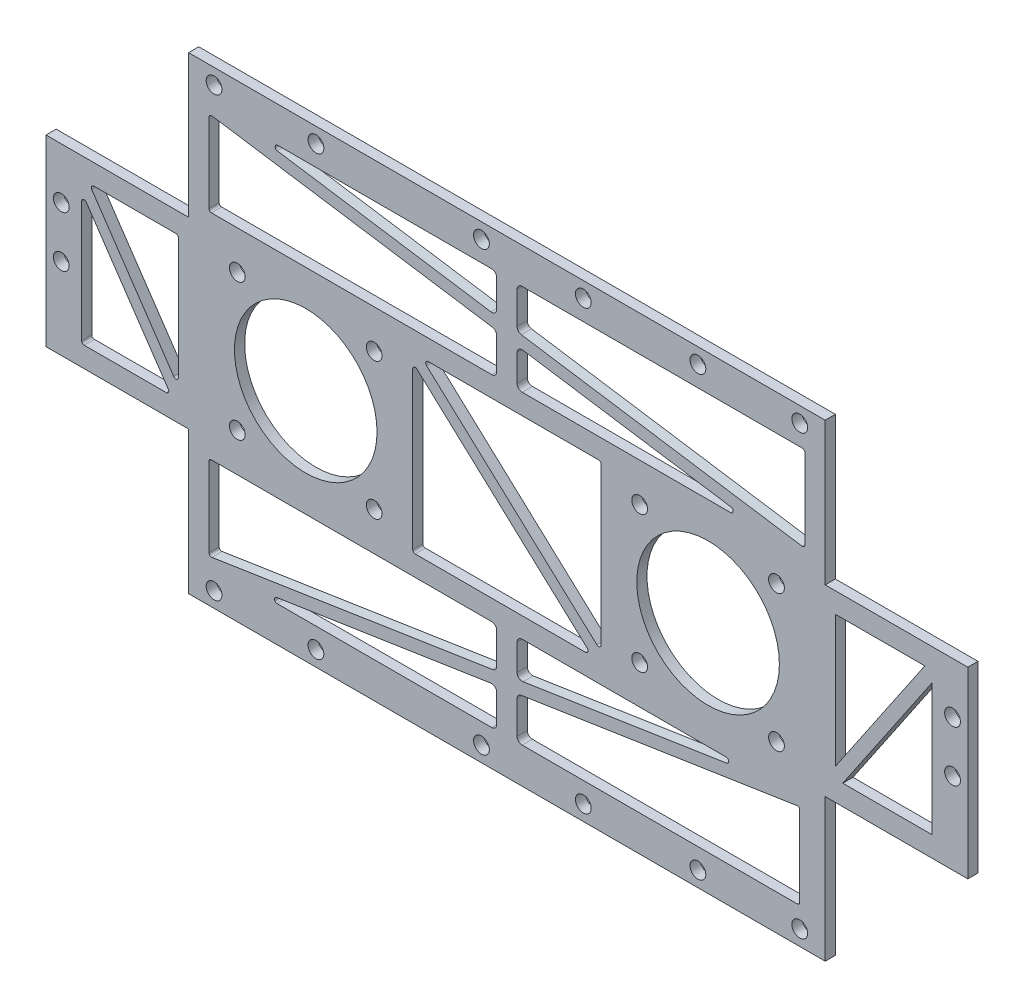
SolidWorks part; units mm, degrees
material "Thornel Mat VMA"
ref_plane "前视基准面" through (0, 0, 0) normal (0, 0, 1) x (1, 0, 0)
ref_plane "上视基准面" through (0, 0, 0) normal (0, 1, 0) x (1, 0, 0)
ref_plane "右视基准面" through (0, 0, 0) normal (1, 0, 0) x (0, 0, -1)
sketch "草图1" plane through (0, 0, 0) normal (0, 0, 1) x (1, 0, 0)
  line L0 (-39.5, 0) -> (39.5, 0) construction
  line L7 (-62.5, -32.4324) -> (70.1149, 36.3839) construction
  line L8 (-92.5, -48) -> (-80.6781, -41.8654) construction
  line L9 (-39.5, 0) -> (-52.935, -13.435) construction
  line L10 (-39.5, 0) -> (-39.5, -19) construction
  line L11 (-52.935, 13.435) -> (-26.065, -13.435) construction
  line L12 (-39.5, 0) -> (-26.065, 13.435) construction
  line L13 (26.065, 13.435) -> (39.5, 0) construction
  line L14 (39.5, 0) -> (52.935, -13.435) construction
  line L15 (39.5, 0) -> (39.5, -24.0416) construction
  line L16 (26.065, -13.435) -> (39.5, 0) construction
  line L17 (39.5, 0) -> (52.935, 13.435) construction
  line L18 (39.5, 0) -> (63.5416, 0) construction
  line L19 (-90.5, 18) -> (-90.5, -18)
  line L20 (-62.5, -46) -> (62.5, -46)
  line L21 (90.5, 18) -> (90.5, -18)
  line L22 (-62.5, 46) -> (62.5, 46)
  line L23 (62.5, -46) -> (62.5, 46) construction
  line L24 (-62.5, -46) -> (-62.5, 46) construction
  line L25 (0, 48) -> (0, -63.7675) construction
  line L26 (-81.1063, 14) -> (-65, 14)
  line L27 (-20, -40) -> (20, -40) construction
  line L28 (-20, -40) -> (-20, -46) construction
  line L29 (-20, -46) -> (20, -46) construction
  line L30 (20, -40) -> (20, -46) construction
  line L31 (-20, -40) -> (20, -46) construction
  line L32 (-20, -46) -> (20, -40) construction
  line L33 (-64.5, 13.5) -> (-64.5, -10.2356)
  line L34 (-66.8937, -14) -> (-83, -14)
  line L35 (-83.5, -13.5) -> (-83.5, 10.2356)
  line L36 (90.5, -18) -> (62.5, -18) construction
  line L37 (-45.0121, 39) -> (-3, 39)
  line L38 (-62.5, -18) -> (-90.5, -18) construction
  line L39 (58.5, 38.5) -> (58.5, 22.7959)
  line L40 (43.9401, 21) -> (3, 21)
  line L41 (-58.5, 21.5) -> (-58.5, 37.0407)
  line L42 (-58, -21) -> (-3, -21)
  line L43 (-62.5, 46) -> (-62.5, 18)
  line L44 (-62.5, 18) -> (-90.5, 18)
  line L45 (-90.5, -18) -> (-62.5, -18)
  line L46 (-62.5, -18) -> (-62.5, -46)
  line L47 (62.5, -46) -> (62.5, -18)
  line L48 (62.5, -18) -> (90.5, -18)
  line L49 (90.5, 18) -> (62.5, 18)
  line L50 (62.5, 18) -> (62.5, 46)
  line L51 (-62.5, 32.4324) -> (62.5, -32.4324) construction
  line L52 (57.5, -22.7969) -> (57.5, -38.5)
  line L53 (57, -39) -> (3, -39)
  line L54 (-58.5, -37.0383) -> (-58.5, -21.5)
  line L55 (64.5, 14) -> (82.0498, 14)
  line L56 (83.5, 11.8629) -> (83.5, -14)
  line L57 (83.5, -14) -> (65.9502, -14)
  line L60 (64.5, 14) -> (64.5, -11.8629)
  line L61 (-15.4434, 17) -> (18, 17)
  line L62 (18.5, 16.5) -> (18.5, -14.2318)
  line L63 (15.4434, -17) -> (-18, -17)
  line L64 (-18.5, -16.5) -> (-18.5, 14.2318)
  line L65 (-17.6617, 14.5999) -> (15.7817, -16.1318)
  line L66 (2, -22) -> (2, -27.1536)
  line L67 (0, 29.9183) -> (47.4731, 22.681) construction
  line L68 (48.1242, -22.4415) -> (0, -29.8407) construction
  line L69 (2, -31.6053) -> (2, -38)
  line L70 (-81.52, 13.2192) -> (-65.4137, -10.5163)
  line L71 (-66.48, -13.2192) -> (-82.5863, 10.5163)
  line L72 (17.6617, -14.5999) -> (-15.7817, 16.1318)
  line L73 (-57.9246, 37.535) -> (-2.8493, 29.1388)
  line L74 (57.9246, 22.3016) -> (2.8493, 30.6978)
  line L75 (-57.924, -37.5325) -> (-2.848, -29.0645)
  line L76 (56.924, -22.3027) -> (2.848, -30.6169)
  line L77 (83.5, 11.8629) -> (65.9502, -14)
  line L78 (82.0498, 14) -> (64.5, -11.8629)
  line L79 (-2, -38) -> (-2, -32.5278)
  line L80 (-2, -28.0761) -> (-2, -22)
  line L81 (-2, 38) -> (-2, 32.6011)
  line L82 (-2, 28.1502) -> (-2, 22)
  line L83 (2, 38) -> (2, 31.6864)
  line L84 (2, 27.2355) -> (2, 22)
  line L85 (3.152, -28.142) -> (43.1373, -21.9942)
  line L86 (3, -21) -> (43.0613, -21)
  line L87 (-3, -39) -> (-45.1332, -39)
  line L88 (-3.152, -31.5394) -> (-45.2092, -38.0058)
  line L89 (-3, 21) -> (-58, 21)
  line L90 (3.1507, 28.2241) -> (44.0155, 21.9943)
  line L91 (-3.1507, 31.6125) -> (-45.0874, 38.0057)
  line L92 (3, 39) -> (58, 39)
  circle A16 centre (-39.5, 0) radius 19 construction
  circle A30 centre (-52.935, -13.435) radius 1.55
  circle A33 centre (-52.935, 13.435) radius 1.55
  circle A34 centre (-26.065, -13.435) radius 1.55
  circle A35 centre (-26.065, 13.435) radius 1.55
  circle A48 centre (-39.5, 0) radius 14
  circle A49 centre (39.5, 0) radius 14
  circle A50 centre (57.5, -43) radius 1.55
  circle A51 centre (37.5, -43) radius 1.55
  circle A52 centre (-57.5, -43) radius 1.55
  circle A53 centre (-37.5, -43) radius 1.55
  circle A54 centre (-57.5, 43) radius 1.55
  circle A55 centre (-37.5, 43) radius 1.55
  circle A56 centre (37.5, 43) radius 1.55
  circle A57 centre (57.5, 43) radius 1.55
  circle A58 centre (15, -43) radius 1.55
  circle A59 centre (-5, -43) radius 1.55
  circle A60 centre (-5, 43) radius 1.55
  circle A61 centre (15, 43) radius 1.55
  circle A68 centre (-87.5, 8) radius 1.55
  circle A69 centre (-87.5, -2) radius 1.55
  circle A70 centre (87.5, 8) radius 1.55
  circle A71 centre (87.5, -2) radius 1.55
  arc A72 (-81.1063, 14) -> (-81.52, 13.2192) centre (-81.1063, 13.5) ccw
  arc A73 (-65, 14) -> (-64.5, 13.5) centre (-65, 13.5) cw
  arc A74 (-64.5, -10.2356) -> (-65.4137, -10.5163) centre (-65, -10.2356) cw
  arc A75 (-66.48, -13.2192) -> (-66.8937, -14) centre (-66.8937, -13.5) cw
  arc A76 (-83, -14) -> (-83.5, -13.5) centre (-83, -13.5) cw
  arc A77 (-83.5, 10.2356) -> (-82.5863, 10.5163) centre (-83, 10.2356) cw
  arc A78 (17.6617, -14.5999) -> (18.5, -14.2318) centre (18, -14.2318) ccw
  arc A79 (18.5, 16.5) -> (18, 17) centre (18, 16.5) ccw
  arc A80 (-15.4434, 17) -> (-15.7817, 16.1318) centre (-15.4434, 16.5) ccw
  arc A81 (-18.5, 14.2318) -> (-17.6617, 14.5999) centre (-18, 14.2318) cw
  arc A82 (15.7817, -16.1318) -> (15.4434, -17) centre (15.4434, -16.5) cw
  arc A83 (-18, -17) -> (-18.5, -16.5) centre (-18, -16.5) cw
  arc A84 (56.924, -22.3027) -> (57.5, -22.7969) centre (57, -22.7969) cw
  arc A85 (57.5, -38.5) -> (57, -39) centre (57, -38.5) cw
  arc A86 (-45.2092, -38.0058) -> (-45.1332, -39) centre (-45.1332, -38.5) ccw
  arc A87 (-58, -21) -> (-58.5, -21.5) centre (-58, -21.5) ccw
  arc A88 (43.1373, -21.9942) -> (43.0613, -21) centre (43.0613, -21.5) ccw
  arc A89 (-58.5, -37.0383) -> (-57.924, -37.5325) centre (-58, -37.0383) ccw
  arc A90 (57.9246, 22.3016) -> (58.5, 22.7959) centre (58, 22.7959) ccw
  arc A91 (58.5, 38.5) -> (58, 39) centre (58, 38.5) ccw
  arc A92 (-45.0121, 39) -> (-45.0874, 38.0057) centre (-45.0121, 38.5) ccw
  arc A93 (-58.5, 37.0407) -> (-57.9246, 37.535) centre (-58, 37.0407) cw
  arc A94 (-58.5, 21.5) -> (-58, 21) centre (-58, 21.5) ccw
  arc A95 (44.0155, 21.9943) -> (43.9401, 21) centre (43.9401, 21.5) cw
  arc A96 (-2, 38) -> (-3, 39) centre (-3, 38) ccw
  arc A97 (3, 39) -> (2, 38) centre (3, 38) ccw
  arc A98 (2, 31.6864) -> (2.8493, 30.6978) centre (3, 31.6864) ccw
  arc A99 (-3.1507, 31.6125) -> (-2, 32.6011) centre (-3, 32.6011) ccw
  arc A100 (-2, 28.1502) -> (-2.8493, 29.1388) centre (-3, 28.1502) ccw
  arc A101 (3.1507, 28.2241) -> (2, 27.2355) centre (3, 27.2355) ccw
  arc A102 (2, 22) -> (3, 21) centre (3, 22) ccw
  arc A103 (-3, 21) -> (-2, 22) centre (-3, 22) ccw
  arc A104 (2.848, -30.6169) -> (2, -31.6053) centre (3, -31.6053) ccw
  arc A105 (2, -38) -> (3, -39) centre (3, -38) ccw
  arc A106 (-3, -39) -> (-2, -38) centre (-3, -38) ccw
  arc A107 (-2, -32.5278) -> (-3.152, -31.5394) centre (-3, -32.5278) ccw
  arc A108 (-2.848, -29.0645) -> (-2, -28.0761) centre (-3, -28.0761) ccw
  arc A109 (2, -27.1536) -> (3.152, -28.142) centre (3, -27.1536) ccw
  arc A110 (3, -21) -> (2, -22) centre (3, -22) ccw
  arc A111 (-2, -22) -> (-3, -21) centre (-3, -22) ccw
  circle A112 centre (39.5, 0) radius 19 construction
  circle A113 centre (26.065, 13.435) radius 1.55
  circle A114 centre (52.935, 13.435) radius 1.55
  circle A115 centre (52.935, -13.435) radius 1.55
  circle A116 centre (26.065, -13.435) radius 1.55
  point P0 (0, 0)
  point P9 (0, 0)
  point P51 (-39.5, 0)
  point P77 (0, -43)
  point P190 (2, 39)
  point P193 (2, 30.8273)
  point P196 (-2, 31.4371)
  point P201 (2, 28.3995)
  point P206 (-2, 21)
  point P213 (-2, -39)
  point P216 (-2, -31.3623)
  point P221 (2, -28.3191)
  point P224 (2, -21)
  dimension "D4" = 3
  dimension "D5" = 45
  dimension "D6" = 45
  dimension "D8" = 45
  dimension "D12" = 5
  dimension "D20" = 5
  dimension "D16" = 5
  dimension "D30" = 5
  dimension "D32" = 4
  dimension "D34" = 2
  dimension "D36" = 4
  dimension "D40" = 0.5
  dimension "D44" = 4
  dimension "D42" = 0.5
  dimension "D49" = 0.5
  dimension "D50" = 0.5
  dimension "D59" = 1
  dimension "D60" = 1
  dimension "D7" = 45
  dimension "D9" = 45
  dimension "D10" = 45
  dimension "D11" = 45
  dimension "D13" = 3
  dimension "D14" = 20
  dimension "D15" = 10
  dimension "D17" = 20
  dimension "D18" = 10
  dimension "D19" = 3
  dimension "D21" = 20
  dimension "D22" = 3
  dimension "D23" = 10
  dimension "D24" = 10
  dimension "D25" = 7
  dimension "D26" = 5
  dimension "D27" = 20
  dimension "D28" = 40
  dimension "D29" = 6
  dimension "D31" = 20
  dimension "D33" = 4
  dimension "D35" = 4
  dimension "D37" = 2
  dimension "D38" = 7
  dimension "D39" = 7
  dimension "D41" = 4
  dimension "D43" = 7
  dimension "D45" = 21
  dimension "D46" = 21
  dimension "D47" = 1.2
  dimension "D48" = 1.2
  dimension "D51" = 1.2
  dimension "D52" = 1.2
  dimension "D53" = 4
  dimension "D54" = 4
  dimension "D55" = 2
  dimension "D56" = 2
  dimension "D57" = 2
  dimension "D58" = 2
extrude "凸台-拉伸1" add sketch "草图1" along normal blind 2
